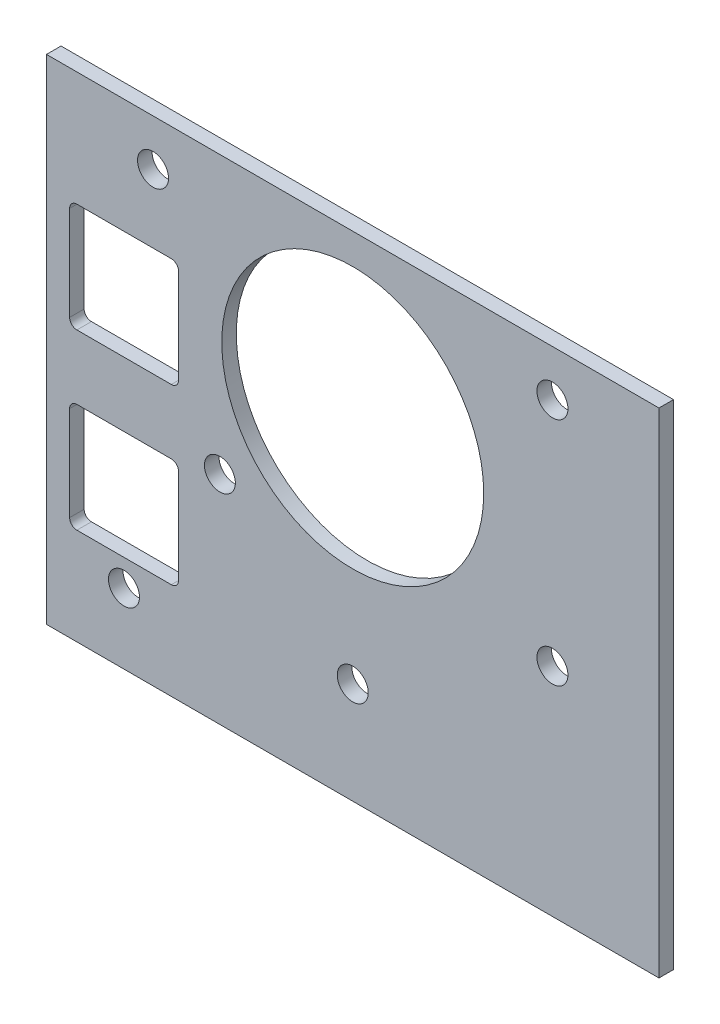
SolidWorks part; units mm, degrees
ref_plane "Front Plane" through (0, 0, 0) normal (0, 0, 1) x (1, 0, 0)
ref_plane "Top Plane" through (0, 0, 0) normal (0, 1, 0) x (1, 0, 0)
ref_plane "Right Plane" through (0, 0, 0) normal (1, 0, 0) x (0, 0, -1)
ref_plane "Plane1" through (0, 0, -1.0174) normal (0, 0, -1) x (-1, 0, 0)
sketch "Sketch1" plane through (0, 0, -1.0174) normal (0, 0, -1) x (-1, 0, 0)
  line L0 (118.3565, -137.9301) -> (124.8565, -137.9301)
  line L1 (125.3565, -138.4301) -> (125.3565, -144.9301)
  line L2 (124.8565, -145.4301) -> (118.3565, -145.4301)
  line L3 (117.8565, -144.9301) -> (117.8565, -138.4301)
  line L8 (124.8565, -157.3681) -> (118.3565, -157.3681)
  line L9 (117.8565, -156.8681) -> (117.8565, -150.3681)
  line L10 (118.3565, -149.8681) -> (124.8565, -149.8681)
  line L11 (125.3565, -150.3681) -> (125.3565, -156.8681)
  line L12 (117.8565, -141.6801) -> (125.3565, -141.6801) construction
  line L14 (126.9484, -130.0469) -> (84.7844, -130.0469)
  line L15 (121.6065, -149.8681) -> (121.6065, -157.3681) construction
  line L16 (121.6065, -157.3681) -> (121.6065, -153.6181) construction
  line L17 (121.6065, -153.6181) -> (125.3565, -153.6181) construction
  line L18 (126.9484, -130.0469) -> (126.9484, -164.0321)
  line L19 (126.9484, -164.0321) -> (84.7844, -164.0321)
  line L20 (84.7844, -130.0469) -> (84.7844, -164.0321)
  arc A0 (117.8565, -138.4301) -> (118.3565, -137.9301) centre (118.3565, -138.4301) cw
  arc A1 (124.8565, -137.9301) -> (125.3565, -138.4301) centre (124.8565, -138.4301) cw
  arc A2 (125.3565, -144.9301) -> (124.8565, -145.4301) centre (124.8565, -144.9301) cw
  arc A3 (118.3565, -145.4301) -> (117.8565, -144.9301) centre (118.3565, -144.9301) cw
  circle A4 centre (105.8664, -141.169) radius 9.017
  circle A5 centre (92.1183, -149.1065) radius 1.0668
  circle A6 centre (92.1183, -133.2315) radius 1.0668
  circle A7 centre (119.6146, -133.2315) radius 1.0668
  circle A8 centre (105.8664, -157.044) radius 1.0668
  circle A14 centre (115.0104, -149.1065) radius 1.0633
  circle A40 centre (121.6144, -159.203) radius 1.0668
  arc A43 (125.3565, -156.8681) -> (124.8565, -157.3681) centre (124.8565, -156.8681) cw
  arc A44 (118.3565, -157.3681) -> (117.8565, -156.8681) centre (118.3565, -156.8681) cw
  arc A45 (117.8565, -150.3681) -> (118.3565, -149.8681) centre (118.3565, -150.3681) cw
  arc A46 (124.8565, -149.8681) -> (125.3565, -150.3681) centre (124.8565, -150.3681) cw
  point P24 (0, 0)
  point P25 (0, 0)
  point P26 (0, 0)
  dimension "D1" = 33.9852
  dimension "D2" = 7.5
  dimension "D3" = 6.5
  dimension "D4" = 7.5
  dimension "D5" = 7.5
  dimension "D6" = 42.164
  dimension "D7" = 10.414
  dimension "D8" = 5.3419
  dimension "D9" = 22.352
  dimension "D10" = 3.1845
  dimension "D11" = 3.1845
  dimension "D12" = 7.3338
  dimension "D13" = 7.3338
  dimension "D14" = 21.082
  dimension "D15" = 22.8632
  dimension "D16" = 7.3338
  dimension "D17" = 14.9257
  dimension "D18" = 6.9882
  dimension "D19" = 21.082
  dimension "D20" = 5.334
  dimension "D21" = 4.8292
  dimension "D22" = 14.9257
  dimension "D23" = 11.938
extrude "Boss-Extrude1" add sketch "Sketch1" against normal blind 1
